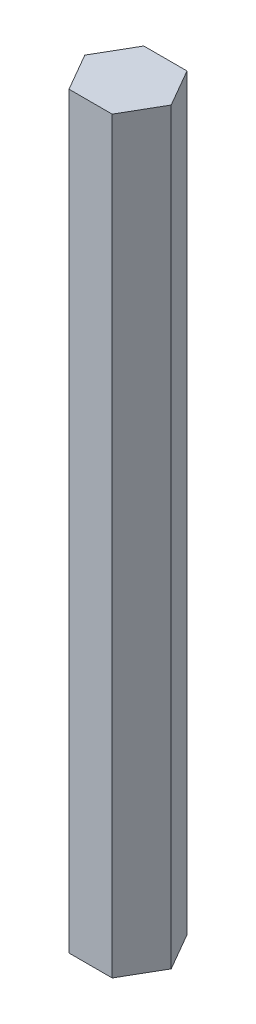
SolidWorks part; units mm, degrees
ref_plane "Front Plane" through (0, 0, 0) normal (0, 0, 1) x (1, 0, 0)
ref_plane "Top Plane" through (0, 0, 0) normal (0, 1, 0) x (1, 0, 0)
ref_plane "Right Plane" through (0, 0, 0) normal (1, 0, 0) x (0, 0, -1)
sketch "Sketch1" plane through (0, 0, 0) normal (0, 1, 0) x (1, 0, 0)
  line L1 (3.6662, 6.35) -> (-3.6662, 6.35)
  line L2 (-3.6662, 6.35) -> (-7.3323, 0)
  line L3 (-7.3323, 0) -> (-3.6662, -6.35)
  line L4 (-3.6662, -6.35) -> (3.6662, -6.35)
  line L5 (3.6662, -6.35) -> (7.3323, 0)
  line L6 (7.3323, 0) -> (3.6662, 6.35)
  circle A0 centre (0, 0) radius 6.35 construction
  dimension "D1" = 12.7
extrude "Boss-Extrude1" add sketch "Sketch1" along normal blind 127
